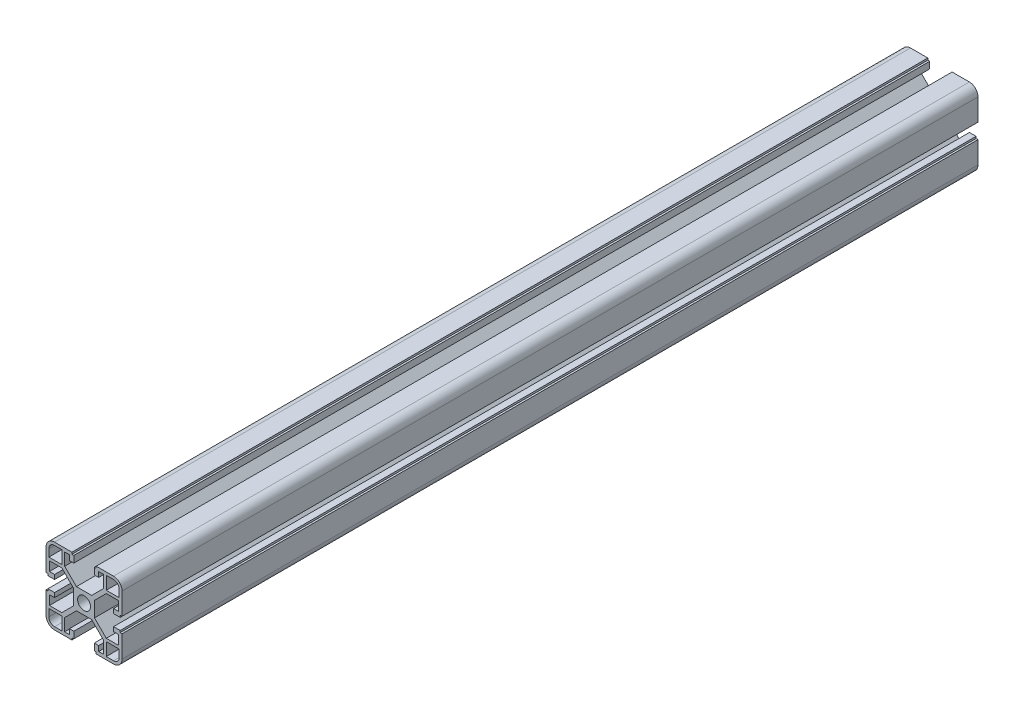
SolidWorks part; units mm, degrees
material "6061-T6 (SS)"
ref_plane "Front Plane" through (0, 0, 0) normal (0, 0, 1) x (1, 0, 0)
ref_plane "Top Plane" through (0, 0, 0) normal (0, 1, 0) x (1, 0, 0)
ref_plane "Right Plane" through (0, 0, 0) normal (1, 0, 0) x (0, 0, -1)
sketch "Sketch1" plane through (0, 0, 0) normal (0, 0, 1) x (1, 0, 0)
  line L0 (3.4, 0) -> (5.5, 0)
  line L1 (10.19, 11.69) -> (4, 5.5)
  line L2 (11.69, 10.19) -> (5.5, 4)
  line L3 (18.2, 10.19) -> (11.69, 10.19)
  line L4 (18.2, 10.19) -> (18.2, 5.2656)
  line L5 (18.2, 5.2656) -> (15.5, 5.2656)
  line L6 (15.5, 5.2656) -> (15.5, 2.9656)
  line L7 (15.5, 2.9656) -> (19, 2.9656)
  line L8 (19, 2.9656) -> (19, 3.9656)
  line L9 (19, 3.9656) -> (20, 3.9656)
  line L10 (20, 3.9656) -> (20, 15.5)
  line L11 (15.5, 20) -> (6.3853, 20)
  line L12 (18.5, 11.69) -> (18.5, 15.5)
  line L13 (15.5, 18.5) -> (11.69, 18.5)
  line L14 (11.69, 11.69) -> (11.69, 18.5)
  line L15 (0, 3.4) -> (0, 5.5)
  line L16 (4, 5.5) -> (0, 5.5)
  line L17 (6.3853, 20) -> (6.3853, 19)
  line L18 (5.5, 0) -> (5.5, 4)
  line L19 (6.3853, 19) -> (5.3853, 19)
  line L20 (5.3853, 19) -> (5.3853, 15.5)
  line L21 (5.3853, 15.5) -> (7.6853, 15.5)
  line L22 (10.19, 11.69) -> (10.19, 18.2)
  line L23 (11.69, 11.69) -> (18.5, 11.69)
  line L24 (7.6853, 18.2) -> (7.6853, 15.5)
  line L25 (10.19, 18.2) -> (7.6853, 18.2)
  arc A0 (20, 15.5) -> (15.5, 20) centre (15.5, 15.5) ccw
  arc A1 (18.5, 15.5) -> (15.5, 18.5) centre (15.5, 15.5) ccw
  arc A2 (3.4, 0) -> (0, 3.4) centre (0, 0) ccw
  dimension "D3" = 4.5
  dimension "D18" = 1.5
  dimension "D9" = 3.4
  dimension "D20" = 1.8
  dimension "D25" = 3
  dimension "D1" = 5.5
  dimension "D2" = 1.5
  dimension "D4" = 14.5
  dimension "D5" = 1.5
  dimension "D6" = 2.1
  dimension "D7" = 2.3
  dimension "D8" = 1.8
  dimension "D10" = 6.81
  dimension "D11" = 2.1
  dimension "D12" = 1
  dimension "D13" = 4.5
  dimension "D14" = 45
  dimension "D15" = 14.5
  dimension "D16" = 1
  dimension "D17" = 1.5
  dimension "D19" = 6.81
  dimension "D21" = 4.5
  dimension "D22" = 2.3
  dimension "D23" = 1
  dimension "D24" = 1
  dimension "D26" = 8.754
  dimension "D27" = 8.754
  dimension "D28" = 4.9244
  dimension "D29" = 2.5047
extrude "Boss-Extrude1" add sketch "Sketch1" along normal blind 450
mirror "Mirror1" about plane through (0, 0, 0) normal (0, 1, 0) of "Boss-Extrude1"
mirror "Mirror2" about plane through (0, 0, 0) normal (1, 0, 0) of "Boss-Extrude1"
mirror "Mirror3" about plane through (0, 0, 0) normal (0, 1, 0) of "Mirror2"
